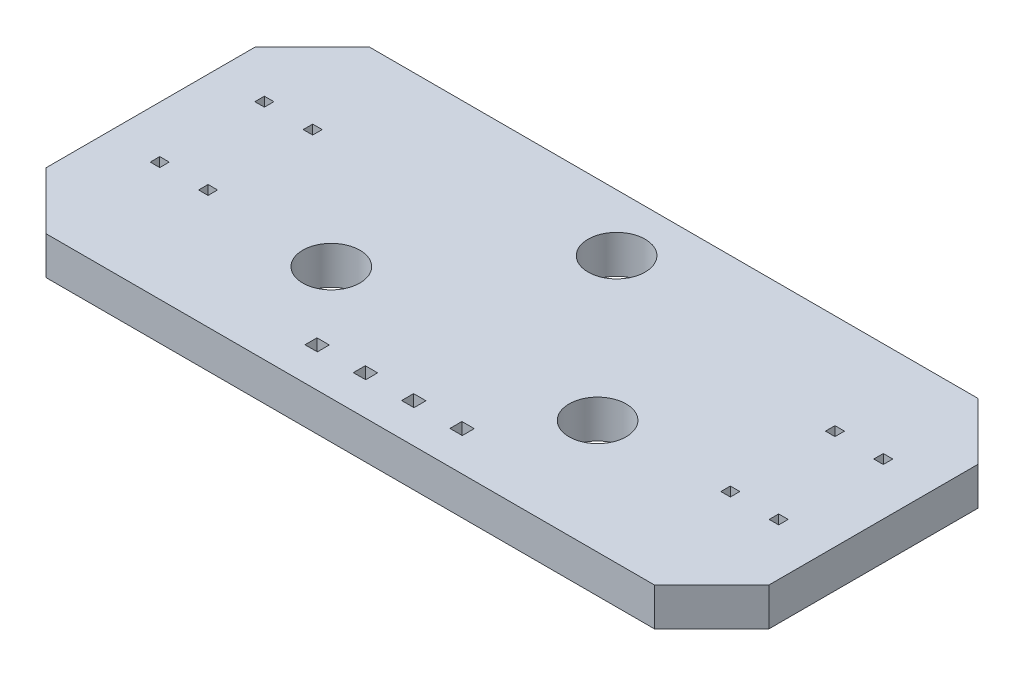
SolidWorks part; units mm, degrees
material "Epoxy, Unfilled"
ref_plane "Front Plane" through (0, 0, 0) normal (0, 0, 1) x (1, 0, 0)
ref_plane "Top Plane" through (0, 0, 0) normal (0, 1, 0) x (1, 0, 0)
ref_plane "Right Plane" through (0, 0, 0) normal (1, 0, 0) x (0, 0, -1)
sketch "Sketch1" plane through (0, 0, 0) normal (0, 1, 0) x (1, 0, 0)
  line L0 (0, 10.9534) -> (0, -10.9534) construction
  line L1 (-21.932, 0) -> (21.932, 0) construction
  line L2 (-19, 5) -> (-19, -6)
  line L3 (-19, -6) -> (-16, -9)
  line L4 (-16, -9) -> (16, -9)
  line L5 (-19, 5) -> (-16, 8)
  line L6 (-16, 8) -> (16, 8)
  line L7 (19, 5) -> (16, 8)
  line L8 (19, -6) -> (16, -9)
  line L9 (19, 5) -> (19, -6)
  line L10 (-16.27, 2.75) -> (-16.27, -2.75) construction
  line L11 (-15, 8) -> (-15, -9) construction
  line L12 (-13.73, 2.75) -> (-13.73, -2.75) construction
  line L13 (-16.52, -3) -> (-16.02, -2.5) construction
  line L14 (-16.52, 2.5) -> (-16.02, 2.5)
  line L15 (-16.52, 2.5) -> (-16.52, 3)
  line L16 (-16.52, 3) -> (-16.02, 3)
  line L17 (-16.02, 2.5) -> (-16.02, 3)
  line L18 (-16.52, 2.5) -> (-16.02, 3) construction
  line L19 (-16.52, 3) -> (-16.02, 2.5) construction
  line L20 (-16.52, -2.5) -> (-16.02, -3) construction
  line L21 (-16.02, -2.5) -> (-16.02, -3)
  line L22 (-16.52, -3) -> (-16.02, -3)
  line L23 (-16.52, -2.5) -> (-16.52, -3)
  line L24 (-16.52, -2.5) -> (-16.02, -2.5)
  line L25 (-13.48, -2.5) -> (-13.98, -3) construction
  line L26 (-13.48, 3) -> (-13.98, 2.5) construction
  line L27 (-13.48, 2.5) -> (-13.98, 3) construction
  line L28 (-13.48, -3) -> (-13.98, -2.5) construction
  line L29 (-13.48, -2.5) -> (-13.98, -2.5)
  line L30 (-13.48, -2.5) -> (-13.48, -3)
  line L31 (-13.48, -3) -> (-13.98, -3)
  line L32 (-13.98, -2.5) -> (-13.98, -3)
  line L33 (-13.98, 2.5) -> (-13.98, 3)
  line L34 (-13.48, 3) -> (-13.98, 3)
  line L35 (-13.48, 2.5) -> (-13.48, 3)
  line L36 (-13.48, 2.5) -> (-13.98, 2.5)
  line L37 (13.48, -3) -> (13.98, -2.5) construction
  line L38 (13.48, 2.5) -> (13.98, 3) construction
  line L39 (13.48, 3) -> (13.98, 2.5) construction
  line L40 (13.48, -2.5) -> (13.98, -3) construction
  line L41 (16.52, -2.5) -> (16.02, -3) construction
  line L42 (16.52, 3) -> (16.02, 2.5) construction
  line L43 (16.52, 2.5) -> (16.02, 3) construction
  line L44 (16.52, -3) -> (16.02, -2.5) construction
  line L45 (13.73, 2.75) -> (13.73, -2.75) construction
  line L46 (15, 8) -> (15, -9) construction
  line L47 (16.27, 2.75) -> (16.27, -2.75) construction
  line L48 (13.48, 2.5) -> (13.98, 2.5)
  line L49 (13.48, 2.5) -> (13.48, 3)
  line L50 (13.48, 3) -> (13.98, 3)
  line L51 (13.98, 2.5) -> (13.98, 3)
  line L52 (13.98, -2.5) -> (13.98, -3)
  line L53 (13.48, -3) -> (13.98, -3)
  line L54 (13.48, -2.5) -> (13.48, -3)
  line L55 (13.48, -2.5) -> (13.98, -2.5)
  line L56 (16.52, -2.5) -> (16.02, -2.5)
  line L57 (16.52, -2.5) -> (16.52, -3)
  line L58 (16.52, -3) -> (16.02, -3)
  line L59 (16.02, -2.5) -> (16.02, -3)
  line L60 (16.02, 2.5) -> (16.02, 3)
  line L61 (16.52, 3) -> (16.02, 3)
  line L62 (16.52, 2.5) -> (16.52, 3)
  line L63 (16.52, 2.5) -> (16.02, 2.5)
  line L64 (-3.81, -6.934) -> (3.81, -6.934) construction
  line L65 (-4.135, -7.249) -> (-3.485, -7.249)
  line L66 (-4.135, -7.249) -> (-4.135, -6.619)
  line L67 (-4.135, -6.619) -> (-3.485, -6.619)
  line L68 (-3.485, -7.249) -> (-3.485, -6.619)
  line L69 (-4.135, -7.249) -> (-3.485, -6.619) construction
  line L70 (-4.135, -6.619) -> (-3.485, -7.249) construction
  line L71 (-2.54, -6.1454) -> (-2.54, -7.5449) construction
  line L72 (-0.945, -6.619) -> (-1.595, -7.249) construction
  line L73 (-0.945, -7.249) -> (-1.595, -6.619) construction
  line L74 (-1.595, -7.249) -> (-1.595, -6.619)
  line L75 (-0.945, -6.619) -> (-1.595, -6.619)
  line L76 (-0.945, -7.249) -> (-0.945, -6.619)
  line L77 (-0.945, -7.249) -> (-1.595, -7.249)
  line L78 (0.945, -7.249) -> (1.595, -6.619) construction
  line L79 (0.945, -6.619) -> (1.595, -7.249) construction
  line L80 (4.135, -6.619) -> (3.485, -7.249) construction
  line L81 (4.135, -7.249) -> (3.485, -6.619) construction
  line L82 (0.945, -7.249) -> (1.595, -7.249)
  line L83 (0.945, -7.249) -> (0.945, -6.619)
  line L84 (0.945, -6.619) -> (1.595, -6.619)
  line L85 (1.595, -7.249) -> (1.595, -6.619)
  line L86 (3.485, -7.249) -> (3.485, -6.619)
  line L87 (4.135, -6.619) -> (3.485, -6.619)
  line L88 (4.135, -7.249) -> (4.135, -6.619)
  line L89 (4.135, -7.249) -> (3.485, -7.249)
  circle A0 centre (-7, -3) radius 1.5
  circle A1 centre (7, -3) radius 1.5
  circle A2 centre (0, 5) radius 1.5
  point P5 (0, 0)
  point P6 (0, 0)
  point P14 (0, 8)
  point P16 (0, -9)
  point P61 (-3.81, -6.934)
  point P74 (-1.27, -6.934)
  point P83 (1.27, -6.934)
  point P84 (3.81, -6.934)
  dimension "D6" = 2.75
  dimension "D16" = 3
  dimension "D18" = 3
  dimension "D19" = 5
  dimension "D1" = 9
  dimension "D2" = 16
  dimension "D3" = 11
  dimension "D4" = 19
  dimension "D5" = 8
  dimension "D7" = 2.75
  dimension "D8" = 2.54
  dimension "D9" = 16.27
  dimension "D10" = 0.5
  dimension "D11" = 0.65
  dimension "D12" = 0.63
  dimension "D13" = 2.54
  dimension "D14" = 2.54
  dimension "D15" = 6.934
  dimension "D17" = 7
extrude "Boss-Extrude1" add sketch "Sketch1" along normal blind 2
